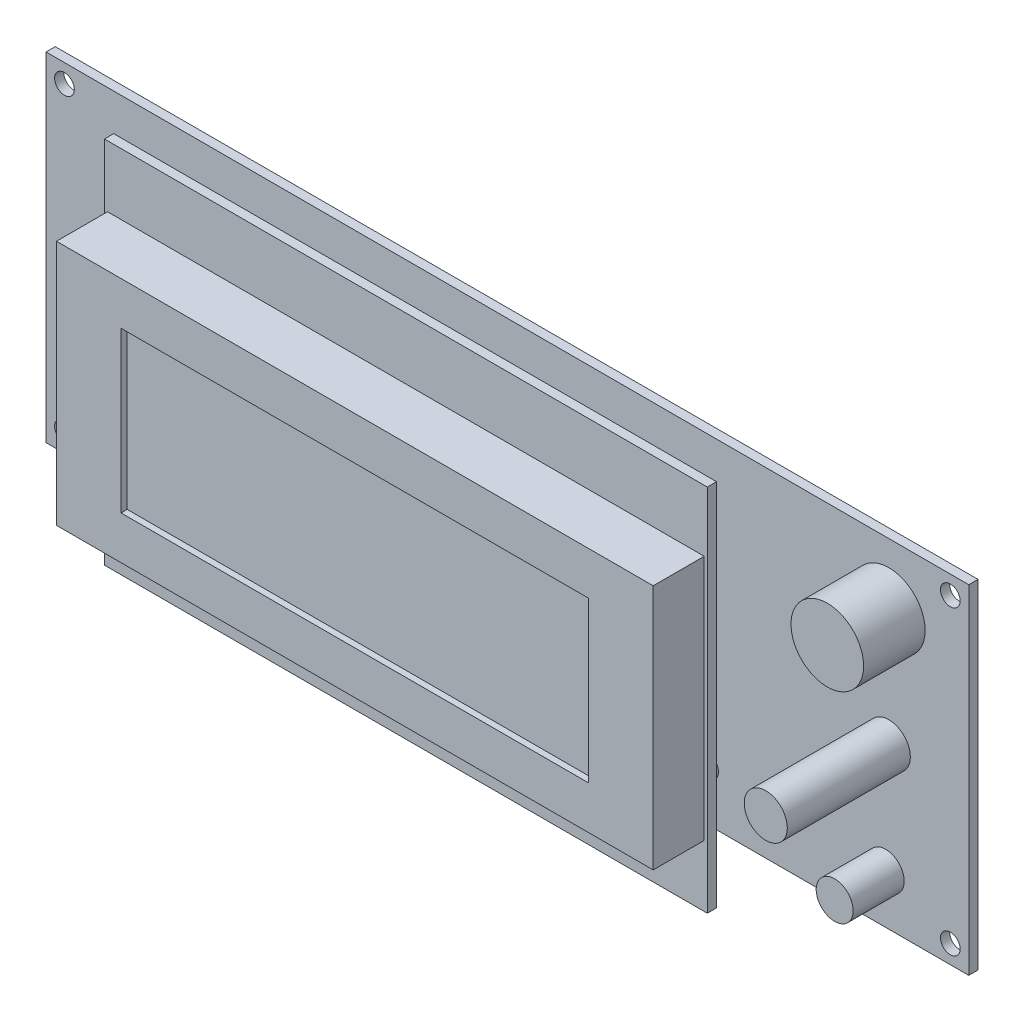
SolidWorks part; units mm, degrees
ref_plane "Plano frontal" through (0, 0, 0) normal (0, 0, 1) x (1, 0, 0)
ref_plane "Plano superior" through (0, 0, 0) normal (0, 1, 0) x (1, 0, 0)
ref_plane "Plano direito" through (0, 0, 0) normal (1, 0, 0) x (0, 0, -1)
sketch "Esboço1" plane through (0, 0, 0) normal (0, 0, 1) x (1, 0, 0)
  line L1 (-75, 27.5) -> (75, 27.5)
  line L2 (-75, 27.5) -> (-75, -27.5)
  line L3 (-75, -27.5) -> (75, -27.5)
  line L4 (75, 27.5) -> (75, -27.5)
  line L5 (-75, 27.5) -> (75, -27.5) construction
  line L6 (-75, -27.5) -> (75, 27.5) construction
  point P0 (0, 0)
  dimension "D1" = 150
  dimension "D2" = 55
extrude "Ressalto-extrusão1" add sketch "Esboço1" along normal blind 1.5
sketch "Esboço3" plane through (0, 0, 1.5) normal (0, 0, 1) x (1, 0, 0)
  line L1 (-61, 24.5) -> (37, 24.5)
  line L2 (-61, 24.5) -> (-61, -35.5)
  line L3 (-61, -35.5) -> (37, -35.5)
  line L4 (37, 24.5) -> (37, -35.5)
  line L5 (-61, 24.5) -> (37, -35.5) construction
  line L6 (-61, -35.5) -> (37, 24.5) construction
  line L9 (75, -27.5) -> (75, 27.5) construction
  line L10 (-75, 27.5) -> (-75, -27.5) construction
  line L12 (75, 27.5) -> (-75, 27.5) construction
  point P0 (-12, -5.5)
  dimension "D1" = 60
  dimension "D2" = 38
  dimension "D3" = 14
  dimension "D4" = 3
extrude "Ressalto-extrusão2" add sketch "Esboço3" along normal blind 1.5 from offset 3 separate body
sketch "Esboço4" plane through (0, 0, 6) normal (0, 0, 1) x (1, 0, 0)
  line L0 (37, 24.5) -> (-61, 24.5) construction
  line L1 (-60.5, 14.5) -> (36.5, 14.5)
  line L2 (-60.5, 14.5) -> (-60.5, -25.5)
  line L3 (-60.5, -25.5) -> (36.5, -25.5)
  line L4 (36.5, 14.5) -> (36.5, -25.5)
  line L5 (-60.5, 14.5) -> (36.5, -25.5) construction
  line L6 (-60.5, -25.5) -> (36.5, 14.5) construction
  point P0 (-12, -5.5)
  point P9 (-12, 24.5)
  dimension "D1" = 40
  dimension "D2" = 97
  dimension "D3" = 10
extrude "Ressalto-extrusão3" add sketch "Esboço4" along normal blind 8.3
sketch "Esboço5" plane through (0, 0, 14.3) normal (0, 0, 1) x (1, 0, 0)
  line L0 (36.5, -25.5) -> (36.5, 14.5) construction
  line L1 (-50, 7.5) -> (26, 7.5)
  line L2 (-50, 7.5) -> (-50, -18.5)
  line L3 (-50, -18.5) -> (26, -18.5)
  line L4 (26, 7.5) -> (26, -18.5)
  line L5 (-50, 7.5) -> (26, -18.5) construction
  line L6 (-50, -18.5) -> (26, 7.5) construction
  line L7 (36.5, 14.5) -> (-60.5, 14.5) construction
  point P0 (-12, -5.5)
  point P7 (36.5, -5.5)
  point P11 (-12, 14.5)
  dimension "D1" = 76
  dimension "D2" = 26
extrude "Corte-extrusão1" cut sketch "Esboço5" against normal blind 1
sketch "Esboço6" plane through (0, 0, 1.5) normal (0, 0, 1) x (1, 0, 0)
  line L0 (75, -27.5) -> (75, 27.5) construction
  line L2 (-75, -27.5) -> (75, -27.5) construction
  circle A0 centre (62, -1.5) radius 3.5
  dimension "D3" = 7
  dimension "D1" = 13
  dimension "D2" = 26
extrude "Ressalto-extrusão4" add sketch "Esboço6" along normal blind 20
sketch "Esboço7" plane through (0, 0, 1.5) normal (0, 0, 1) x (1, 0, 0)
  line L0 (75, -27.5) -> (75, 27.5) construction
  line L1 (-75, -27.5) -> (75, -27.5) construction
  circle A0 centre (32.3, -19.2) radius 2
  dimension "D3" = 4
  dimension "D1" = 42.7
  dimension "D2" = 8.3
extrude "Ressalto-extrusão5" add sketch "Esboço7" along normal blind 4.5
sketch "Esboço8" plane through (0, 0, 1.5) normal (0, 0, 1) x (1, 0, 0)
  line L1 (75, -27.5) -> (75, 27.5) construction
  line L2 (75, 27.5) -> (-75, 27.5) construction
  circle A0 centre (62, 17.5) radius 5.9
  dimension "D3" = 11.8
  dimension "D1" = 10
  dimension "D2" = 13
extrude "Ressalto-extrusão6" add sketch "Esboço8" along normal blind 10
sketch "Esboço9" plane through (0, 0, 1.5) normal (0, 0, 1) x (1, 0, 0)
  line L1 (-75, -27.5) -> (75, -27.5) construction
  line L2 (75, -27.5) -> (75, 27.5) construction
  circle A0 centre (61.5, -19.5) radius 3
  dimension "D3" = 6
  dimension "D1" = 13.5
  dimension "D2" = 8
extrude "Ressalto-extrusão7" add sketch "Esboço9" along normal blind 8.3
sketch "Esboço11" plane through (0, 0, 0) normal (0, 0, -1) x (-1, 0, 0)
  line L0 (-75, 27.5) -> (75, 27.5) construction
  line L1 (-24.0887, 5.5) -> (-3.7887, 5.5)
  line L2 (-24.0887, 5.5) -> (-24.0887, -3.1)
  line L3 (-24.0887, -3.1) -> (-3.7887, -3.1)
  line L4 (-3.7887, 5.5) -> (-3.7887, -3.1)
  line L5 (-24.0887, 5.5) -> (-3.7887, -3.1) construction
  line L6 (-24.0887, -3.1) -> (-3.7887, 5.5) construction
  line L7 (9.7, 5.5) -> (30, 5.5)
  line L8 (9.7, 5.5) -> (9.7, -3.1)
  line L9 (9.7, -3.1) -> (30, -3.1)
  line L10 (30, 5.5) -> (30, -3.1)
  line L11 (9.7, 5.5) -> (30, -3.1) construction
  line L12 (9.7, -3.1) -> (30, 5.5) construction
  line L13 (75, 27.5) -> (75, -27.5) construction
  point P0 (-13.9387, 1.2)
  point P5 (19.85, 1.2)
  dimension "D1" = 13.4887
  dimension "D2" = 22
  dimension "D3" = 20.3
  dimension "D4" = 45
  dimension "D5" = 8.6
extrude "Ressalto-extrusão8" add sketch "Esboço11" along normal blind 15
sketch "Esboço12" plane through (0, 0, 0) normal (0, 0, -1) x (-1, 0, 0)
  line L0 (75, 27.5) -> (75, -27.5) construction
  line L1 (74.9, 5.5) -> (49.4, 5.5)
  line L2 (74.9, 5.5) -> (74.9, -21)
  line L3 (74.9, -21) -> (49.4, -21)
  line L4 (49.4, 5.5) -> (49.4, -21)
  line L5 (-75, 27.5) -> (75, 27.5) construction
  dimension "D1" = 26.5
  dimension "D2" = 25.5
  dimension "D3" = 0.1
  dimension "D4" = 22
extrude "Ressalto-extrusão9" add sketch "Esboço12" along normal blind 3
sketch "Esboço13" plane through (0, 0, 1.5) normal (0, 0, 1) x (1, 0, 0)
  line L0 (-83.7542, 0) -> (0, 0) construction
  line L1 (0, 0) -> (0, 37.6212) construction
  line L2 (75, 27.5) -> (-75, 27.5) construction
  line L3 (-75, 27.5) -> (-75, -27.5) construction
  circle A0 centre (-72, 24.5) radius 1.6
  circle A1 centre (-72, -24.5) radius 1.6
  circle A2 centre (72, -24.5) radius 1.6
  circle A3 centre (72, 24.5) radius 1.6
  dimension "D1" = 3.2
  dimension "D2" = 3
  dimension "D3" = 3
extrude "Corte-extrusão2" cut sketch "Esboço13" against normal blind 10
